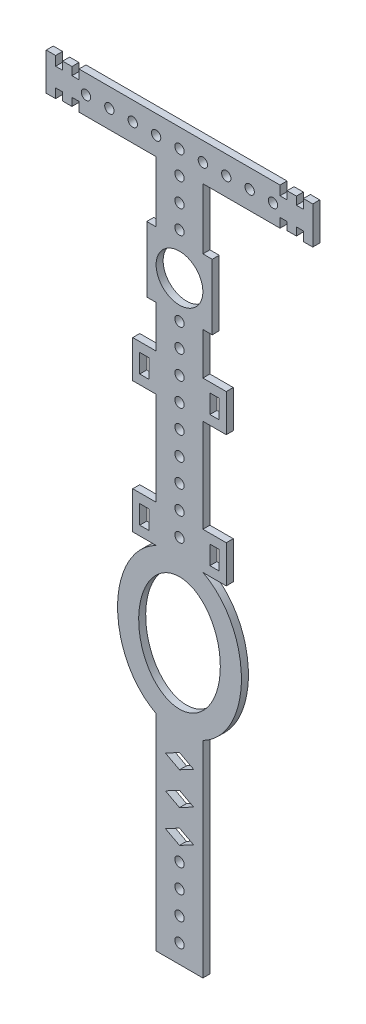
SolidWorks part; units mm, degrees
ref_plane "前视基准面" through (0, 0, 0) normal (0, 0, 1) x (1, 0, 0)
ref_plane "上视基准面" through (0, 0, 0) normal (0, 1, 0) x (1, 0, 0)
ref_plane "右视基准面" through (0, 0, 0) normal (1, 0, 0) x (0, 0, -1)
other "Configuration Table"
sketch "草图1" plane through (0, 0, 0) normal (0, 0, 1) x (1, 0, 0)
  line L0 (-21.4993, 30) -> (-21.4993, 28)
  line L1 (-21.4993, 28) -> (-22.9993, 28)
  line L2 (-22.9993, 29.7) -> (-24.9993, 29.7)
  line L3 (-7, 9) -> (-5, 9)
  line L4 (-7, 9) -> (-7, -5)
  line L5 (-7, -5) -> (-5, -5)
  line L6 (7, 9) -> (7, -5)
  line L7 (-7, 9) -> (7, -5) construction
  line L8 (-7, -5) -> (7, 9) construction
  line L9 (-24.9993, 29.7) -> (-24.9993, 28)
  line L10 (-26.4993, 28) -> (-26.4993, 30.4519)
  line L12 (-26.4993, 30) -> (-28.4993, 30)
  line L13 (-28.4993, 30) -> (-28.4993, 22)
  line L18 (-22.9993, 24) -> (-22.9993, 22.3)
  line L19 (-26.4993, 24) -> (-24.9993, 24)
  line L20 (0, -0.8258) -> (0, -11.7354) construction
  line L21 (-5, 9) -> (-5, 22)
  line L22 (-5, 22) -> (-21.4993, 22)
  line L23 (-26.4993, 22) -> (-28.4993, 22)
  line L24 (-26.4993, 24) -> (-26.4993, 22)
  line L26 (-24.9993, 22.3) -> (-24.9993, 24)
  line L27 (-22.9993, 22.3) -> (-24.9993, 22.3)
  line L29 (-21.4993, 24) -> (-22.9993, 24)
  line L30 (-21.4993, 22) -> (-21.4993, 24)
  line L35 (22.9993, 28) -> (22.9993, 29.7)
  line L36 (26.4993, 28) -> (24.9993, 28)
  line L42 (-26.4993, 28) -> (-24.9993, 28)
  line L43 (-22.9993, 28) -> (-22.9993, 29.7)
  line L46 (21.4993, 22) -> (21.4993, 24)
  line L47 (21.4993, 24) -> (22.9993, 24)
  line L48 (-21.4993, 30) -> (21.4993, 30)
  line L49 (-5, -5) -> (-5, -14)
  line L50 (-5, -14) -> (-10, -14)
  line L51 (-10, -14) -> (-10, -22)
  line L52 (-10, -22) -> (-5, -22)
  line L53 (-5, -22) -> (-5, -42)
  line L54 (-5, -42) -> (-10, -42)
  line L55 (-10, -42) -> (-10, -50)
  line L56 (-10, -50) -> (-5, -50)
  line L57 (-8.5, -16) -> (-6.5, -16)
  line L58 (-8.5, -16) -> (-8.5, -20)
  line L59 (-8.5, -20) -> (-6.5, -20)
  line L60 (-6.5, -16) -> (-6.5, -20)
  line L61 (-8.5, -16) -> (-6.5, -20) construction
  line L62 (-8.5, -20) -> (-6.5, -16) construction
  line L63 (-8.5, -44) -> (-6.5, -44)
  line L64 (-8.5, -44) -> (-8.5, -48)
  line L65 (-8.5, -48) -> (-6.5, -48)
  line L66 (-6.5, -44) -> (-6.5, -48)
  line L67 (-8.5, -44) -> (-6.5, -48) construction
  line L68 (-8.5, -48) -> (-6.5, -44) construction
  line L69 (5, 9) -> (5, 22)
  line L70 (22.9993, 22.3) -> (24.9993, 22.3)
  line L71 (24.9993, 22.3) -> (24.9993, 24)
  line L72 (26.4993, 24) -> (26.4993, 22)
  line L74 (26.4993, 22) -> (28.4993, 22)
  line L75 (26.4993, 24) -> (24.9993, 24)
  line L76 (22.9993, 24) -> (22.9993, 22.3)
  line L77 (28.4993, 30) -> (28.4993, 22)
  line L78 (26.4993, 30) -> (28.4993, 30)
  line L79 (5, 22) -> (21.4993, 22)
  line L80 (5, -5) -> (5, -14)
  line L81 (8.5, -48) -> (6.5, -44) construction
  line L82 (8.5, -44) -> (6.5, -48) construction
  line L83 (8.5, -20) -> (6.5, -16) construction
  line L84 (8.5, -16) -> (6.5, -20) construction
  line L85 (6.5, -44) -> (6.5, -48)
  line L86 (8.5, -48) -> (6.5, -48)
  line L87 (8.5, -44) -> (8.5, -48)
  line L88 (8.5, -44) -> (6.5, -44)
  line L89 (6.5, -16) -> (6.5, -20)
  line L90 (8.5, -20) -> (6.5, -20)
  line L91 (8.5, -16) -> (8.5, -20)
  line L92 (8.5, -16) -> (6.5, -16)
  line L93 (10, -50) -> (5, -50)
  line L94 (10, -42) -> (10, -50)
  line L95 (5, -42) -> (10, -42)
  line L96 (5, -22) -> (5, -42)
  line L97 (10, -22) -> (5, -22)
  line L98 (10, -14) -> (10, -22)
  line L99 (5, -14) -> (10, -14)
  line L100 (-5, -81.1196) -> (-5, -125.1196)
  line L102 (5, -125.1196) -> (5, -81.1196)
  line L107 (3, -101.4579) -> (0, -103.0613)
  line L108 (0, -103.0613) -> (-3, -101.4579)
  line L109 (-3, -101.4579) -> (0, -99.8545)
  line L110 (0, -99.8545) -> (3, -101.4579)
  line L111 (3, -94.4579) -> (0, -96.0613)
  line L112 (0, -96.0613) -> (-3, -94.4579)
  line L113 (-3, -94.4579) -> (0, -92.8545)
  line L114 (0, -92.8545) -> (3, -94.4579)
  line L115 (3, -87.4579) -> (0, -89.0613)
  line L116 (0, -89.0613) -> (-3, -87.4579)
  line L117 (-3, -87.4579) -> (0, -85.8545)
  line L118 (0, -85.8545) -> (3, -87.4579)
  line L119 (-5, -125.1196) -> (5, -125.1196)
  line L120 (-27.5, 26) -> (-15.7949, 26) construction
  line L121 (26.4993, 28) -> (26.4993, 30)
  line L123 (24.9993, 29.7) -> (24.9993, 28)
  line L124 (22.9993, 29.7) -> (24.9993, 29.7)
  line L125 (21.4993, 28) -> (22.9993, 28)
  line L126 (21.4993, 30) -> (21.4993, 28)
  line L127 (5, -5) -> (7, -5)
  line L128 (5, 9) -> (7, 9)
  circle A0 centre (0, 2) radius 5
  circle A2 centre (0, -121.1196) radius 1
  circle A3 centre (0, -116.1196) radius 1
  circle A4 centre (0, -46) radius 1
  circle A5 centre (0, -41) radius 1
  circle A6 centre (0, -36) radius 1
  circle A7 centre (0, -31) radius 1
  circle A8 centre (0, -26) radius 1
  circle A9 centre (0, -21) radius 1
  circle A10 centre (0, -16) radius 1
  circle A11 centre (0, -11) radius 1
  circle A12 centre (0, -6) radius 1
  circle A13 centre (0, 25.9514) radius 1
  circle A14 centre (5, 25.9514) radius 1
  circle A15 centre (10, 25.9514) radius 1
  circle A16 centre (15, 25.9514) radius 1
  circle A17 centre (20, 25.9514) radius 1
  circle A18 centre (-5, 25.9514) radius 1
  circle A19 centre (-10, 25.9514) radius 1
  circle A20 centre (-15, 25.9514) radius 1
  circle A21 centre (-20, 25.9514) radius 1
  circle A22 centre (0, 20.9514) radius 1
  circle A23 centre (0, 15.9514) radius 1
  circle A24 centre (0, 10.9514) radius 1
  circle A25 centre (0, -111.1196) radius 1
  circle A26 centre (0, -106.1196) radius 1
  ellipse E0 centre (0, -65.5598) end of major axis (0, -77.8215) minor radius 8.7277
  spline S1 degree 3 poles (-2.9572, -82.0581) (0, -82.472) (2.9572, -82.0581) (6.5802, -80.4965) (10.1362, -77.0656) (12.461, -72.0885) (13.2579, -67.5921) (13.2579, -63.5275) (12.461, -59.0311) (10.1362, -54.0539) (6.5802, -50.6231) (2.9572, -49.0614) (0, -48.6476) (-2.9572, -49.0614) (-6.5802, -50.6231) (-10.1362, -54.0539) (-12.461, -59.0311) (-13.2579, -63.5275) (-13.2579, -67.5921) (-12.461, -72.0885) (-10.1362, -77.0656) (-6.5802, -80.4965) (-2.9572, -82.0581) (0, -82.472) (2.9572, -82.0581) knots -0.785398 -0.392699 -0.19635 0 0.19635 0.392699 0.785398 1.178097 1.472622 1.668971 1.963495 2.356194 2.748894 2.945243 3.141593 3.337942 3.534292 3.926991 4.31969 4.614214 4.810564 5.105088 5.497787 5.890486 6.086836 6.283185 6.479535 6.675884 7.068583 only from (0, -82.334) to (0, -82.334)
  point P0 (-21.4993, 30)
  point P25 (-28.4993, 26)
  point P34 (-21.4993, 22)
  point P42 (-7.5, -46)
  point P45 (-7.5, -18)
  point P66 (-7.5, -18)
  point P72 (-13.2402, -65.5598)
  point P74 (13.2402, -65.5598)
  point P75 (-5, -50)
  point P81 (0, 30)
  point P107 (5, -50)
  point P108 (7.5, -18)
  point P109 (7.5, -46)
  point P182 (21.4993, 22)
  point P183 (28.4993, 26)
  point P184 (21.4993, 30)
  dimension "D1" = 10
  dimension "D38" = 2
  dimension "D40" = 2
  dimension "D2" = 14
  dimension "D3" = 14
  dimension "D5" = 2
  dimension "D6" = 1.7
  dimension "D7" = 1.5
  dimension "D8" = 2
  dimension "D9" = 4
  dimension "D10" = 2
  dimension "D11" = 8
  dimension "D12" = 3
  dimension "D13" = 2
  dimension "D14" = 4
  dimension "D21" = 5
  dimension "D22" = 8
  dimension "D23" = 1.5
  dimension "D24" = 2
  dimension "D25" = 4
  dimension "D26" = 20
  dimension "D27" = 4
  dimension "D28" = 10
  dimension "D39" = 9
  dimension "D41" = 5
  dimension "D42" = 5
extrude "凸台-拉伸1" add sketch "草图1" along normal blind 1.5 contours S1 L93 L94 L95 L96 L97 L98 L99 L80 L127 L6 L128 L69 L79 L46 L47 L76 L70 L71 L75 L72 L74 L77 L78 L121 L36 L123 L124 L35 L125 L126 L48 L0 L1 L43 L2 L9 L42 L10 L12 L13 L23 L24 L19 L26 L27 L18 L29 L30 L22 L21 | S1 E0 | S1 L100 L119 L102 A26 A25 A3 A2 L109 L110 L107 L108 L113 L114 L111 L112 L117 L118 L115 L116
